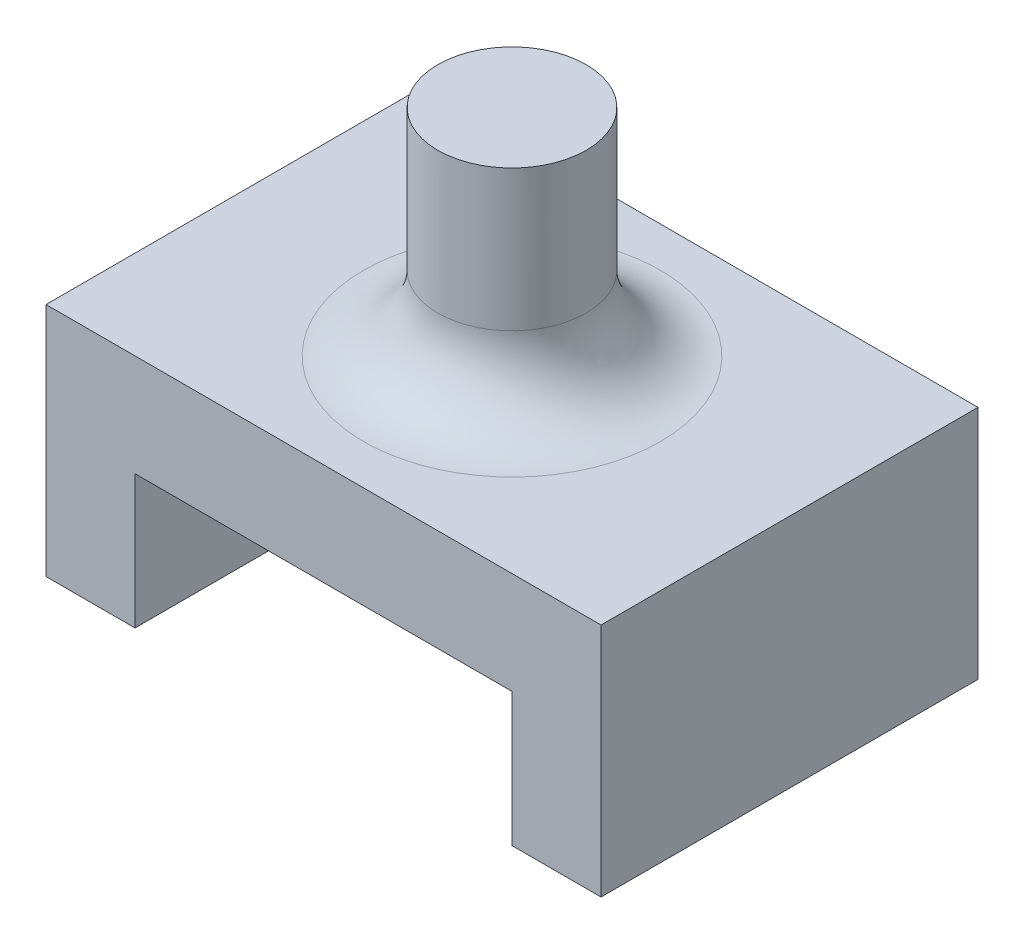
SolidWorks part; units mm, degrees
ref_plane "Front Plane" through (0, 0, 0) normal (0, 0, 1) x (1, 0, 0)
ref_plane "Top Plane" through (0, 0, 0) normal (0, 1, 0) x (1, 0, 0)
ref_plane "Right Plane" through (0, 0, 0) normal (1, 0, 0) x (0, 0, -1)
sketch "Sketch1" plane through (0, 0, 0) normal (0, 0, 1) x (1, 0, 0)
  line L0 (-10.1895, 0) -> (-10.1895, 9)
  line L1 (-10.1895, 9) -> (15.2105, 9)
  line L2 (15.2105, 9) -> (15.2105, 0)
  line L3 (15.2105, 0) -> (21.2105, 0)
  line L4 (21.2105, 0) -> (21.2105, 15.875)
  line L5 (21.2105, 15.875) -> (-16.1895, 15.875)
  line L6 (-16.1895, 15.875) -> (-16.1895, 0)
  line L7 (-16.1895, 0) -> (-10.1895, 0)
  dimension "D1" = 25.4
  dimension "D2" = 9
  dimension "D3" = 15.875
  dimension "D4" = 6
  dimension "D5" = 6
extrude "Boss-Extrude1" add sketch "Sketch1" along normal blind 25.4
sketch "Sketch2" plane through (0, 15.875, 0) normal (0, 1, 0) x (1, 0, 0)
  line L0 (2.5105, -25.4) -> (2.5105, 0) construction
  line L1 (21.2105, -25.4) -> (-16.1895, -25.4) construction
  line L2 (21.2105, 0) -> (-16.1895, 0) construction
  circle A0 centre (2.5105, -12.7) radius 5
  dimension "D1" = 10
extrude "Boss-Extrude2" add sketch "Sketch2" along normal blind 14.5
fillet "Fillet1" radius 5 1 edges at (-2.4895, 15.875, 12.7)
